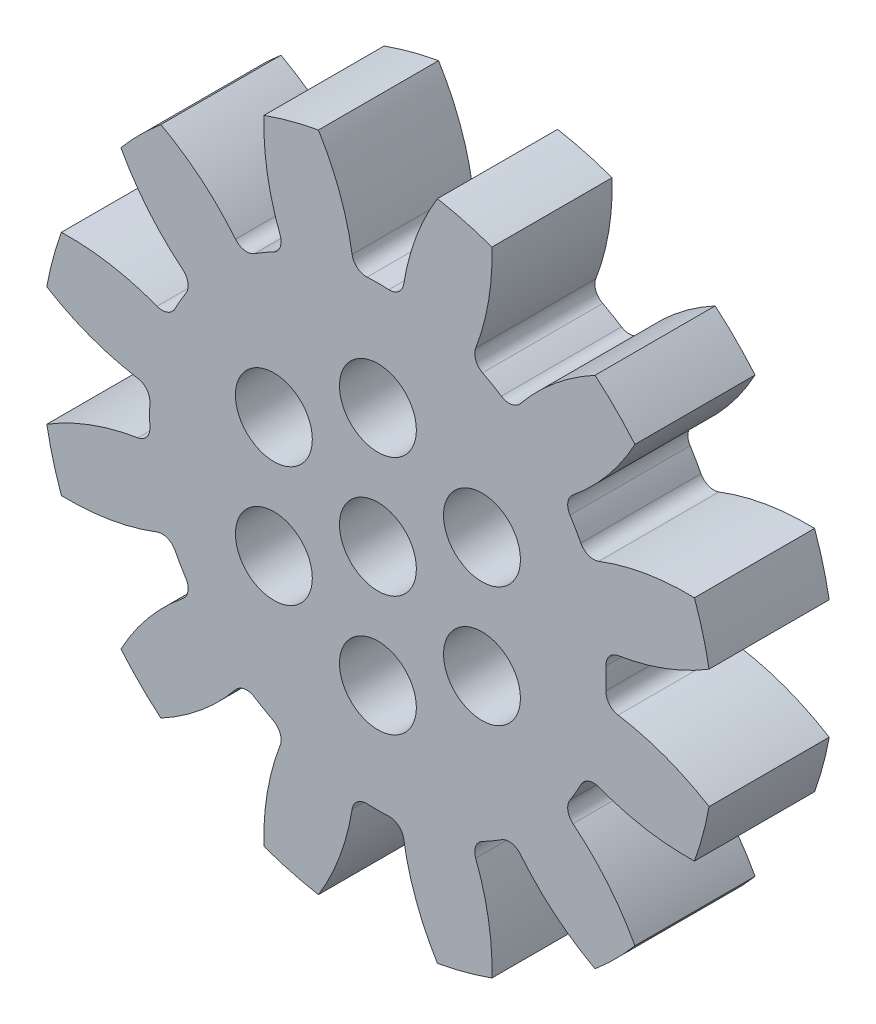
SolidWorks part; units mm, degrees
ref_plane "Front Plane" through (0, 0, 0) normal (0, 0, 1) x (1, 0, 0)
ref_plane "Top Plane" through (0, 0, 0) normal (0, 1, 0) x (1, 0, 0)
ref_plane "Right Plane" through (0, 0, 0) normal (1, 0, 0) x (0, 0, -1)
sketch "Sketch1" plane through (0, 0, 0) normal (0, 0, 1) x (1, 0, 0)
  circle A0 centre (0, 0) radius 12
  circle A1 centre (0, 0) radius 9.5
  circle A2 centre (0, 0) radius 14
  dimension "D1" = 24
  dimension "D2" = 28
  dimension "D3" = 4.5
extrude "Boss-Extrude1" add sketch "Sketch1" along normal mid plane 5 contours A2
sketch "Sketch2" plane through (0, 0, 0) normal (0, 0, 1) x (1, 0, 0)
  line L0 (0, 0) -> (0, 14) construction
  line L1 (-0.9997, 9.4472) -> (0, 0) construction
  line L2 (-1.5663, 11.8973) -> (1.5663, 11.8973) construction
  line L3 (0, 7.5939) -> (-2.7213, 15.0705) construction
  line L4 (0, 0) -> (3.6235, 13.523) construction
  line L5 (1.5663, 11.8973) -> (4.5922, 11.0866) construction
  circle A0 centre (0, 0) radius 14 construction
  arc A1 (-3.3146, 14.9512) -> (-0.9997, 9.4472) centre (-11.2897, 8.3583) cw
  arc A2 (3.3146, 14.9512) -> (0.9997, 9.4472) centre (11.2897, 8.3583) ccw
  arc A3 (3.3146, 14.9512) -> (-3.3146, 14.9512) centre (0, 0) ccw
  arc A4 (0.9997, 9.4472) -> (-0.9997, 9.4472) centre (0, 0) ccw
  circle A6 centre (0, 0) radius 9.5 construction
  circle A7 centre (0, 0) radius 12 construction
  dimension "D1" = 20
  dimension "D2" = 15
extrude "Cut-Extrude1" cut sketch "Sketch2" against normal through all both and the other way through all
fillet "Fillet1" radius 0.6 1 edges at (-0.9997, 9.4472, 0)
fillet "Fillet2" radius 0.6 1 edges at (0.9997, 9.4472, 0)
sketch "Sketch3" plane through (0, 0, 2.5) normal (0, 0, 1) x (1, 0, 0)
pattern_circular "CirPattern2" count 12 over 360 about axis through (0, 0, 0) along (0, 0, 1) of "Fillet1", "Cut-Extrude1", "Fillet2"
sketch "Sketch4" plane through (0, 0, 2.5) normal (0, 0, 1) x (1, 0, 0)
  line L0 (0, 0) -> (0, 8.1574) construction
  circle A0 centre (0, 0) radius 1.5
  circle A1 centre (0, 5) radius 1.5
  circle A2 centre (4.3301, 2.5) radius 1.5
  circle A3 centre (4.3301, -2.5) radius 1.5
  circle A4 centre (0, -5) radius 1.5
  circle A5 centre (-4.3301, -2.5) radius 1.5
  circle A6 centre (-4.3301, 2.5) radius 1.5
  point P18 (0, 0)
  dimension "D1" = 3
  dimension "D2" = 3
  dimension "D3" = 5
  dimension "D4" = 6
extrude "Cut-Extrude2" cut sketch "Sketch4" against normal through all both and the other way through all
sketch "Sketch5" plane through (0, 0, 2.5) normal (0, 0, 1) x (1, 0, 0)
  circle A0 centre (0, 5) radius 1.6
  circle A1 centre (-4.3301, -2.5) radius 1.5
  circle A2 centre (-4.3301, -2.5) radius 1.5 construction
  circle A3 centre (0, -5) radius 1.5
  circle A4 centre (0, -5) radius 1.5 construction
  circle A5 centre (4.3301, -2.5) radius 1.5
  circle A6 centre (4.3301, -2.5) radius 1.5 construction
  circle A7 centre (4.3301, 2.5) radius 1.5
  circle A8 centre (4.3301, 2.5) radius 1.5 construction
  circle A9 centre (0, 5) radius 1.5
  circle A10 centre (0, 5) radius 1.5 construction
  circle A11 centre (0, 0) radius 1.5
  circle A12 centre (0, 0) radius 1.5 construction
  circle A13 centre (-4.3301, 2.5) radius 1.5
  circle A14 centre (-4.3301, 2.5) radius 1.5 construction
  circle A15 centre (4.3301, 2.5) radius 1.6
  circle A16 centre (4.3301, -2.5) radius 1.6
  circle A17 centre (0, -5) radius 1.6
  circle A18 centre (0, 0) radius 1.6
  circle A19 centre (-4.3301, -2.5) radius 1.6
  circle A20 centre (-4.3301, 2.5) radius 1.6
  dimension "D8" = 3.2
  dimension "D1" = 0
  dimension "D2" = 0
  dimension "D3" = 0
  dimension "D4" = 0
  dimension "D5" = 0
  dimension "D6" = 0
  dimension "D7" = 0
extrude "Cut-Extrude3" cut sketch "Sketch5" against normal through all
equation "\"Number of Teeth\"= 12"
equation "\"Module\"= 2mm"
equation "\"D2@Sketch2\"=180 / \"Number of Teeth\""
equation "\"D1@Sketch1\"= \"Module\" * \"Number of Teeth\""
equation "\"D2@Sketch1\"=(\"Number of Teeth\" + 2) * \"Module\""
equation "\"D3@Sketch1\"= \"Module\" * 2.25"
equation "\"D1@CirPattern2\"= \"Number of Teeth\""
